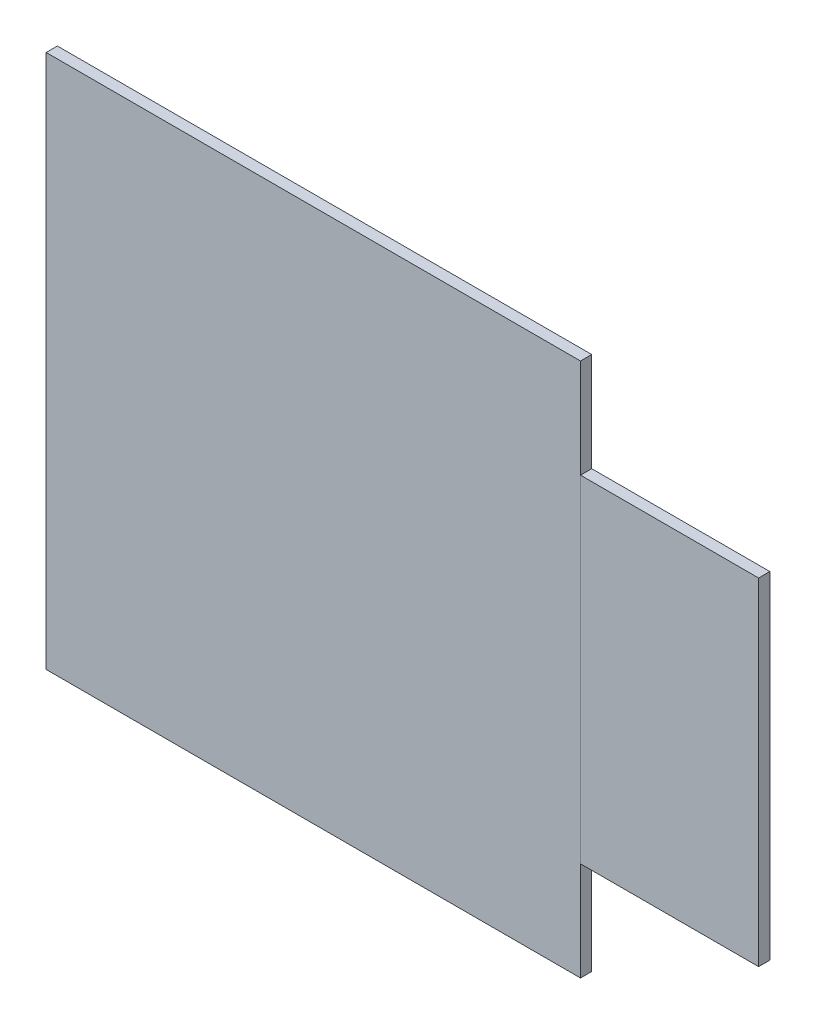
SolidWorks part; units mm, degrees
ref_plane "Front Plane" through (0, 0, 0) normal (0, 0, 1) x (1, 0, 0)
ref_plane "Top Plane" through (0, 0, 0) normal (0, 1, 0) x (1, 0, 0)
ref_plane "Right Plane" through (0, 0, 0) normal (1, 0, 0) x (0, 0, -1)
sketch "Sketch1" plane through (0, 0, 0) normal (0, 0, 1) x (1, 0, 0)
  line L1 (-9.525, 9.525) -> (9.525, 9.525)
  line L2 (-9.525, 9.525) -> (-9.525, -9.525)
  line L3 (-9.525, -9.525) -> (9.525, -9.525)
  line L4 (9.525, 9.525) -> (9.525, -9.525)
  line L5 (-9.525, 9.525) -> (9.525, -9.525) construction
  line L6 (-9.525, -9.525) -> (9.525, 9.525) construction
  point P0 (0, 0)
  dimension "D1" = 19.05
  dimension "D2" = 19.05
extrude "Boss-Extrude1" add sketch "Sketch1" along normal blind 0.4
sketch "Sketch2" plane through (0, 0, 0.4) normal (0, 0, 1) x (1, 0, 0)
  line L0 (9.525, -9.525) -> (9.525, 9.525) construction
  line L1 (15.875, 6) -> (9.525, 6)
  line L2 (15.875, 6) -> (15.875, -6)
  line L3 (15.875, -6) -> (9.525, -6)
  line L4 (9.525, 6) -> (9.525, -6)
  line L5 (15.875, 6) -> (9.525, -6) construction
  line L6 (15.875, -6) -> (9.525, 6) construction
  point P0 (12.7, 0)
  point P7 (0, 0)
  dimension "D1" = 12
  dimension "D2" = 6.35
extrude "Boss-Extrude2" add sketch "Sketch2" against normal up to surface (0.4 mm away) separate body up to face at (0, 0, 0)
